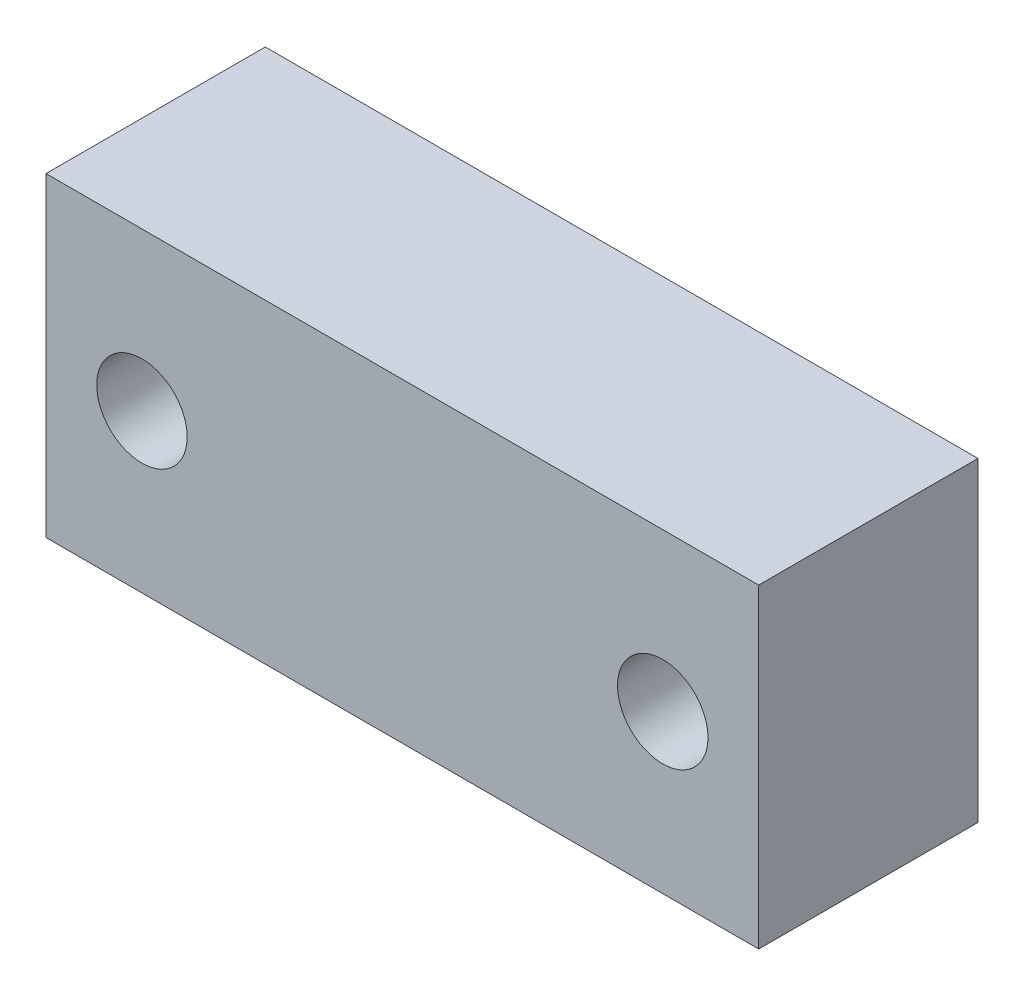
SolidWorks part; units mm, degrees
ref_plane "Front" through (0, 0, 0) normal (0, 0, 1) x (1, 0, 0)
ref_plane "Top" through (0, 0, 0) normal (0, 1, 0) x (1, 0, 0)
ref_plane "Right" through (0, 0, 0) normal (1, 0, 0) x (0, 0, -1)
sketch "草图1" plane through (0, 0, 0) normal (0, 0, 1) x (1, 0, 0)
  line L1 (-26, -11.5) -> (26, -11.5)
  line L2 (-26, -11.5) -> (-26, 11.5)
  line L3 (-26, 11.5) -> (26, 11.5)
  line L4 (26, -11.5) -> (26, 11.5)
  line L5 (-26, -11.5) -> (26, 11.5) construction
  line L6 (-26, 11.5) -> (26, -11.5) construction
  point P0 (0, 0)
  dimension "D1" = 52
  dimension "D2" = 23
extrude "凸台-拉伸1" add sketch "草图1" along normal blind 16
sketch "草图2" plane through (0, 0, 16) normal (0, 0, 1) x (1, 0, 0)
  line L1 (-26, 11.5) -> (-26, -11.5) construction
  line L2 (26, -11.5) -> (26, 11.5) construction
  line L3 (26, 11.5) -> (-26, 11.5) construction
  point P0 (-19, 0)
  point P1 (19, 0)
  dimension "D1" = 7
  dimension "D2" = 7
  dimension "D3" = 11.5
  dimension "D4" = 11.5
hole_wizard "Ø6.6 (6.6) 直径孔1" positions "草图5" profile "草图6" hole size "Ø6.6" standard "GB" end condition up to next
sketch "草图5" plane through (0, 0, 16) normal (0, 0, 1) x (1, 0, 0)
  point P0 (-19, 0)
  point P3 (19, 0)
sketch "草图6" plane through (-19, 0, 16) normal (1, 0, 0) x (0, -1, 0)
  line L0 (0, 0) -> (0, 16)
  line L1 (0, 16) -> (3.3, 16)
  line L2 (3.3, 16) -> (3.3, 0)
  line L5 (3.3, 0) -> (0, 0)
  line L11 (0, -6.35) -> (0, 107.95) construction
  dimension "通孔孔直径" = 6.6
  dimension "通孔孔深度" = 16
